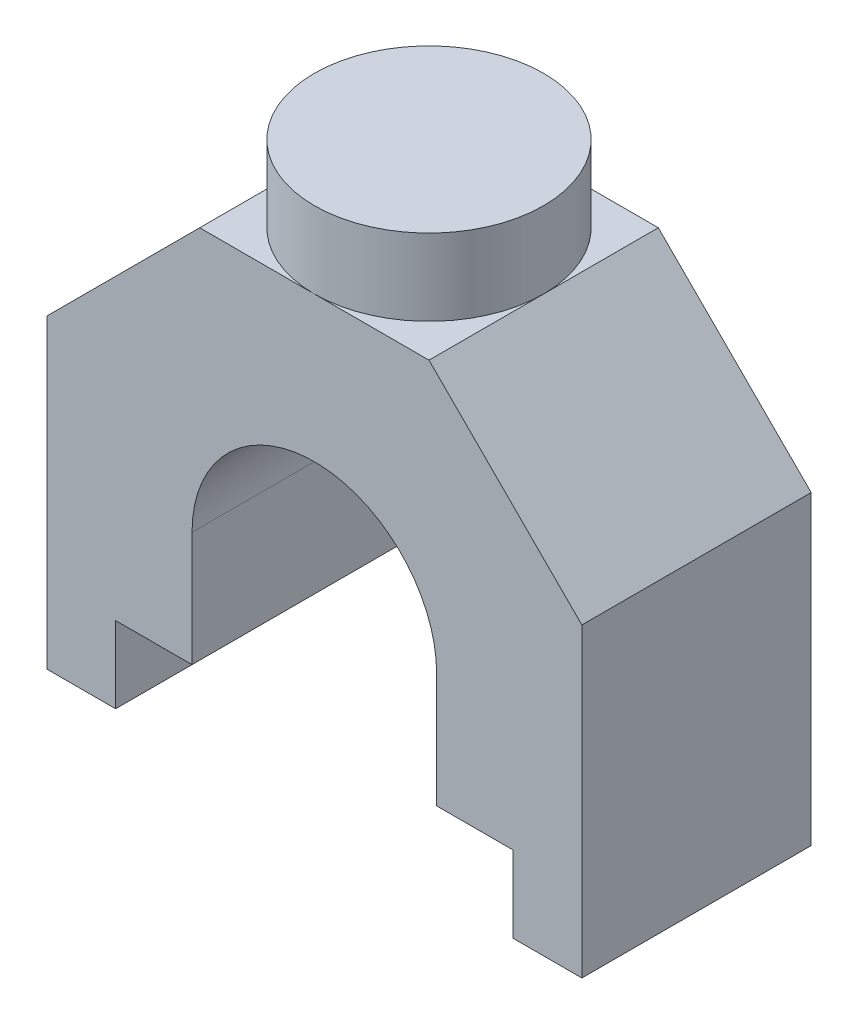
SolidWorks part; units mm, degrees
ref_plane "Front" through (0, 0, 0) normal (0, 0, 1) x (1, 0, 0)
ref_plane "Top" through (0, 0, 0) normal (0, 1, 0) x (1, 0, 0)
ref_plane "Right" through (0, 0, 0) normal (1, 0, 0) x (0, 0, -1)
sketch "草图2" plane through (0, 0, 0) normal (0, 0, 1) x (1, 0, 0)
  line L0 (2, 0) -> (0, -2)
  line L1 (2, 0) -> (5, 0)
  line L2 (0, -2) -> (0, -6)
  line L3 (0, -6) -> (7, -6)
  line L4 (7, -2) -> (7, -6)
  line L5 (1.9, -3.5) -> (5.1, -3.5)
  line L6 (1.9, -3.5) -> (1.9, -6)
  line L7 (1.9, -6) -> (5.1, -6)
  line L8 (5.1, -3.5) -> (5.1, -6)
  line L9 (5, 0) -> (7, -2)
  circle A0 centre (3.5, -3.5) radius 1.6
  arc A1 (5, 0) -> (7, -2) centre (5, -2) cw
  arc A2 (2, 0) -> (0, -2) centre (2, -2) ccw
  point P12 (7, 0)
  point P16 (0, 0)
  dimension "D3" = 3.2
  dimension "D5" = 2
  dimension "D1" = 7
  dimension "D2" = 6
  dimension "D4" = 3.5
extrude "凸台-拉伸1" add sketch "草图2" along normal blind 3 contours A0 L8 L3 L4 L1 L2 L6
sketch "草图4" plane through (0, 0, 0) normal (0, 1, 0) x (1, 0, 0)
  line L0 (2, 0) -> (5, 0) construction
  circle A0 centre (3.5, -1.5) radius 1.5
  dimension "D1" = 3
  dimension "D2" = 1.5
extrude "凸台-拉伸3" add sketch "草图4" along normal blind 1
sketch "草图8" plane through (0, -6, 0) normal (0, -1, 0) x (1, 0, 0)
  line L0 (0, 3) -> (0, 0) construction
  line L1 (0.9, 3.7271) -> (2.6583, 3.7271)
  line L2 (0.9, 3.7271) -> (0.9, -0.5611)
  line L3 (0.9, -0.5611) -> (2.6583, -0.5611)
  line L4 (2.6583, 3.7271) -> (2.6583, -0.5611)
  line L5 (4.5944, 3.9221) -> (6.1, 3.9221)
  line L6 (4.5944, 3.9221) -> (4.5944, -0.8643)
  line L7 (4.5944, -0.8643) -> (6.1, -0.8643)
  line L8 (6.1, 3.9221) -> (6.1, -0.8643)
  line L10 (7, 3) -> (7, 0) construction
  dimension "D1" = 0.9
  dimension "D3" = 0.9
extrude "切除-拉伸3" cut sketch "草图8" against normal blind 1
